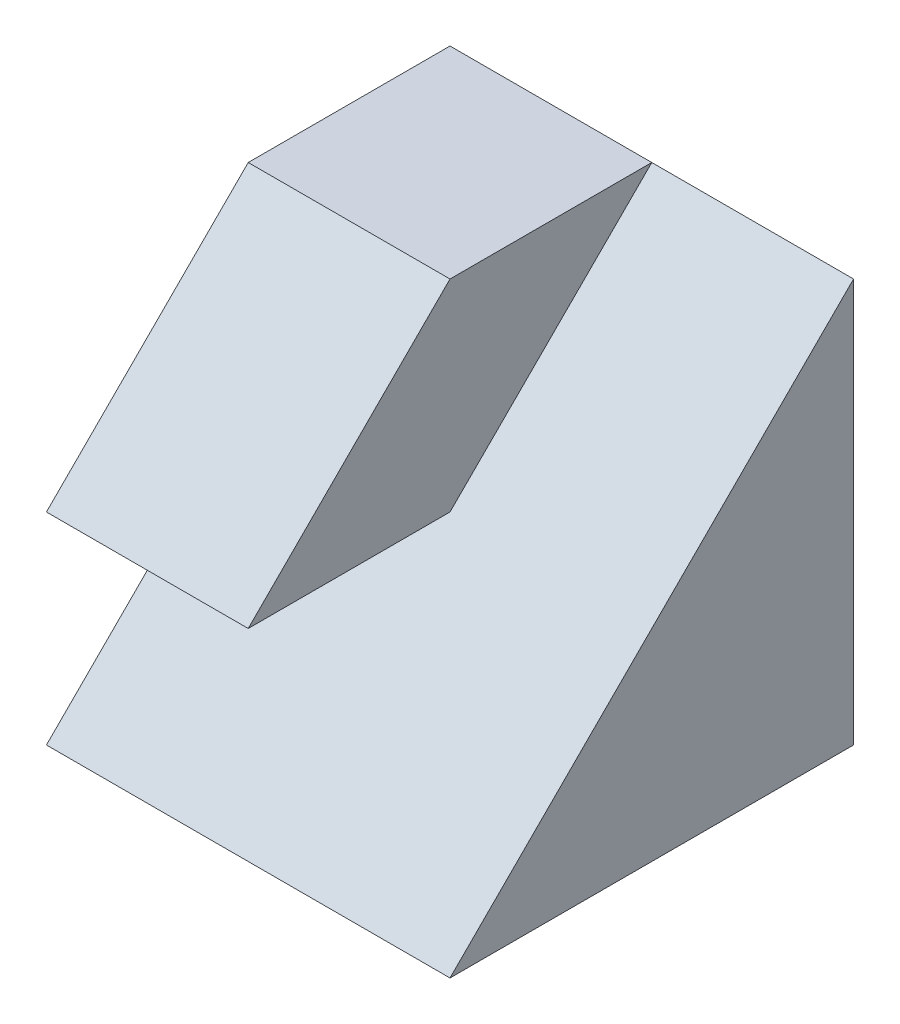
SolidWorks part; units mm, degrees
ref_plane "Front" through (0, 0, 0) normal (0, 0, 1) x (1, 0, 0)
ref_plane "Top" through (0, 0, 0) normal (0, 1, 0) x (1, 0, 0)
ref_plane "Right" through (0, 0, 0) normal (1, 0, 0) x (0, 0, -1)
sketch "Sketch1" plane through (0, 0, 0) normal (0, 1, 0) x (1, 0, 0)
  line L1 (-2, -2) -> (2, -2)
  line L2 (-2, -2) -> (-2, 2)
  line L3 (-2, 2) -> (2, 2)
  line L4 (2, -2) -> (2, 2)
  line L5 (-2, -2) -> (2, 2) construction
  line L6 (-2, 2) -> (2, -2) construction
  point P0 (0, 0)
  dimension "D1" = 4
  dimension "D2" = 4
extrude "Boss-Extrude1" add sketch "Sketch1" along normal blind 4
sketch "Sketch2" plane through (-2, 0, 0) normal (-1, 0, 0) x (0, 0, 1)
  line L0 (2, 0) -> (0, 2)
  line L1 (0, 2) -> (2, 2)
  line L2 (2, 4) -> (2, 0) construction
  line L3 (2, 2) -> (0, 4)
  line L4 (-2, 4) -> (2, 4) construction
  line L5 (0, 4) -> (2, 4)
  line L6 (2, 4) -> (2, 0)
  line M2 (2, 0) -> (2, 4)
  line M3 (2, 4) -> (-2, 4)
extrude "Cut-Extrude1" cut sketch "Sketch2" against normal blind 10 contours L1 L0 M2 | L3 M2 M3
sketch "Sketch3" plane through (2, 0, 0) normal (1, 0, 0) x (0, 0, -1)
  line L0 (-2, 0) -> (2, 4)
  line L1 (2, 4) -> (-2, 4.1166)
  line L2 (-2, 4.1166) -> (-2, 0)
extrude "Cut-Extrude2" cut sketch "Sketch3" against normal blind 2
